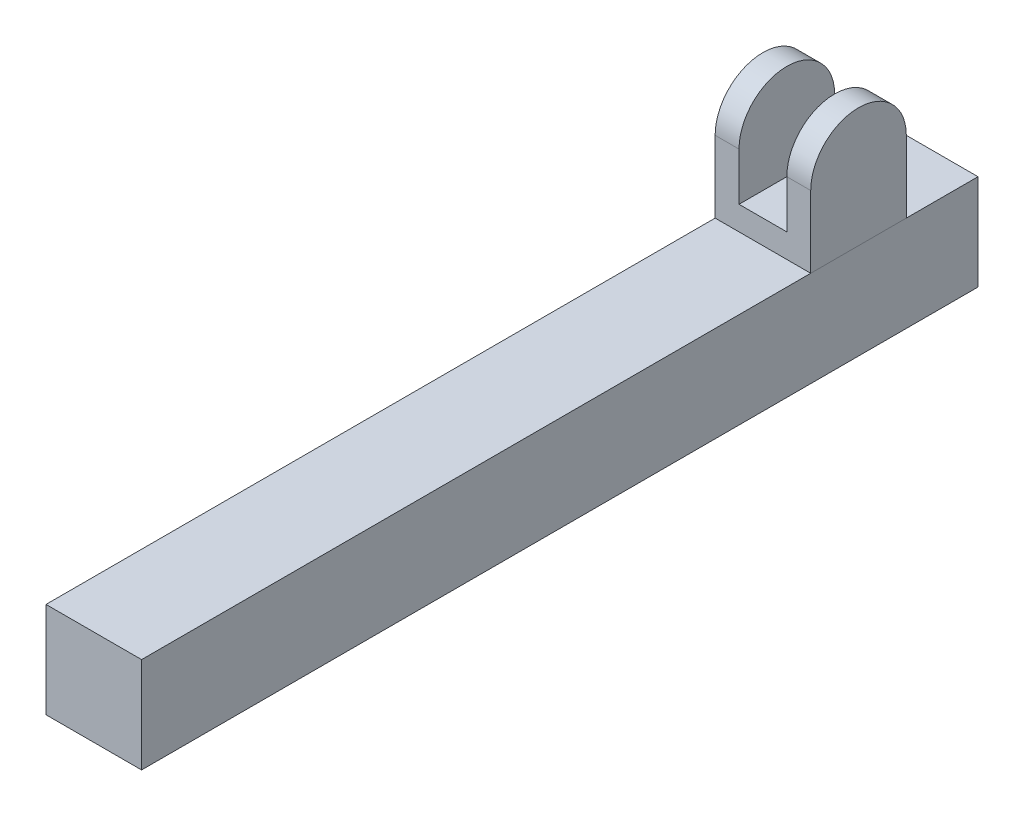
SolidWorks part; units mm, degrees
ref_plane "Front" through (0, 0, 0) normal (0, 0, 1) x (1, 0, 0)
ref_plane "Top" through (0, 0, 0) normal (0, 1, 0) x (1, 0, 0)
ref_plane "Right" through (0, 0, 0) normal (1, 0, 0) x (0, 0, -1)
sketch "草图1" plane through (0, 0, 0) normal (0, 0, 1) x (1, 0, 0)
  line L1 (-4, 4) -> (4, 4)
  line L2 (-4, 4) -> (-4, -4)
  line L3 (-4, -4) -> (4, -4)
  line L4 (4, 4) -> (4, -4)
  dimension "D1" = 8
  dimension "D2" = 8
  dimension "D3" = 4
  dimension "D4" = 4
extrude "凸台-拉伸1" add sketch "草图1" along normal blind 70
sketch "草图2" plane through (0, 0, 0) normal (0, 0, -1) x (-1, 0, 0)
  circle A0 centre (0, 0) radius 3
extrude "切除-拉伸1" cut sketch "草图2" against normal blind 65
sketch "草图3" plane through (-4, 0, 0) normal (-1, 0, 0) x (0, 0, 1)
  line L13 (70, 4) -> (0, 4) construction
  line L14 (6, 4) -> (14, 4)
  line L15 (6, 4) -> (6, 10)
  line L17 (14, 4) -> (14, 10)
  line L18 (0, 4) -> (0, -4) construction
  arc A3 (14, 10) -> (6, 10) centre (10, 10) ccw
  dimension "D1" = 6
extrude "凸台-拉伸2" add sketch "草图3" against normal blind 8 separate body
sketch "草图8" plane through (0, 0, 6) normal (0, 0, -1) x (-1, 0, 0)
  line L0 (4, 14) -> (-4, 14) construction
  line L1 (-2, 14) -> (2, 14)
  line L2 (-2, 14) -> (-2, 6)
  line L3 (-2, 6) -> (2, 6)
  line L4 (2, 14) -> (2, 6)
  dimension "D1" = 4
  dimension "D2" = 2
  dimension "D3" = 8
extrude "切除-拉伸10" cut sketch "草图8" against normal blind 12
